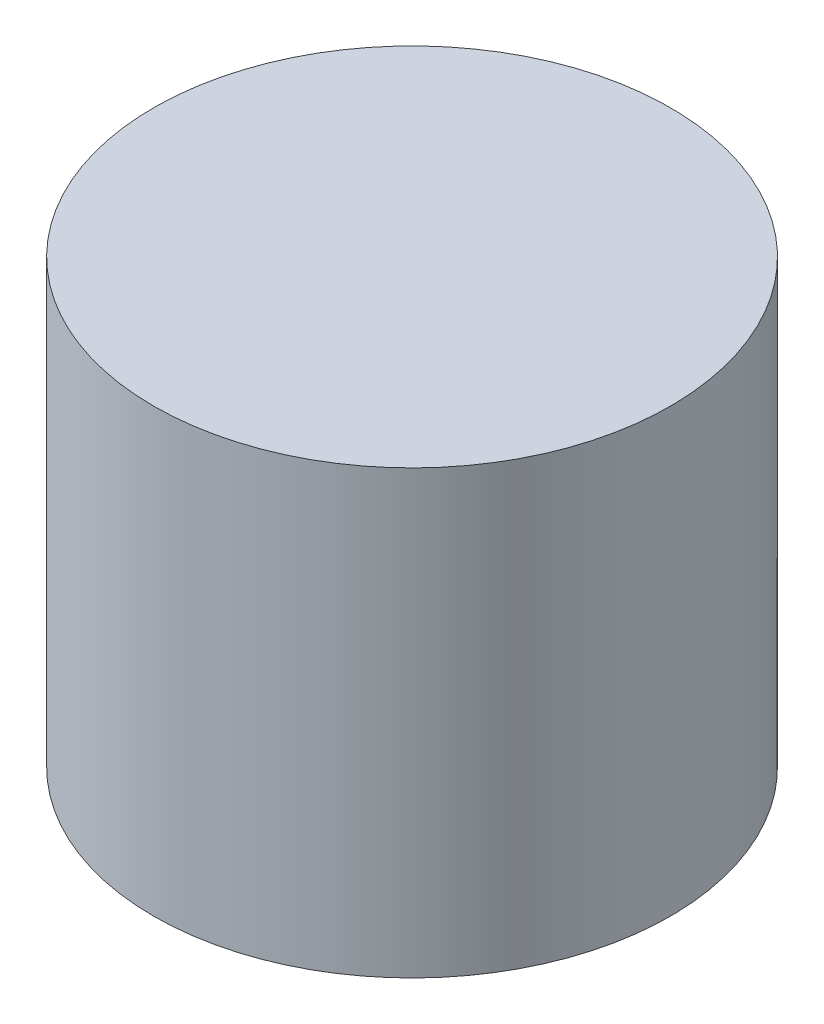
SolidWorks part; units mm, degrees
ref_plane "Front Plane" through (0, 0, 0) normal (0, 0, 1) x (1, 0, 0)
ref_plane "Top Plane" through (0, 0, 0) normal (0, 1, 0) x (1, 0, 0)
ref_plane "Right Plane" through (0, 0, 0) normal (1, 0, 0) x (0, 0, -1)
sketch "Sketch1" plane through (0, 0, 0) normal (0, 1, 0) x (1, 0, 0)
  circle A0 centre (35.691, -14.7929) radius 5.85
  dimension "D1" = 11.7
extrude "Boss-Extrude1" add sketch "Sketch1" along normal blind 10
